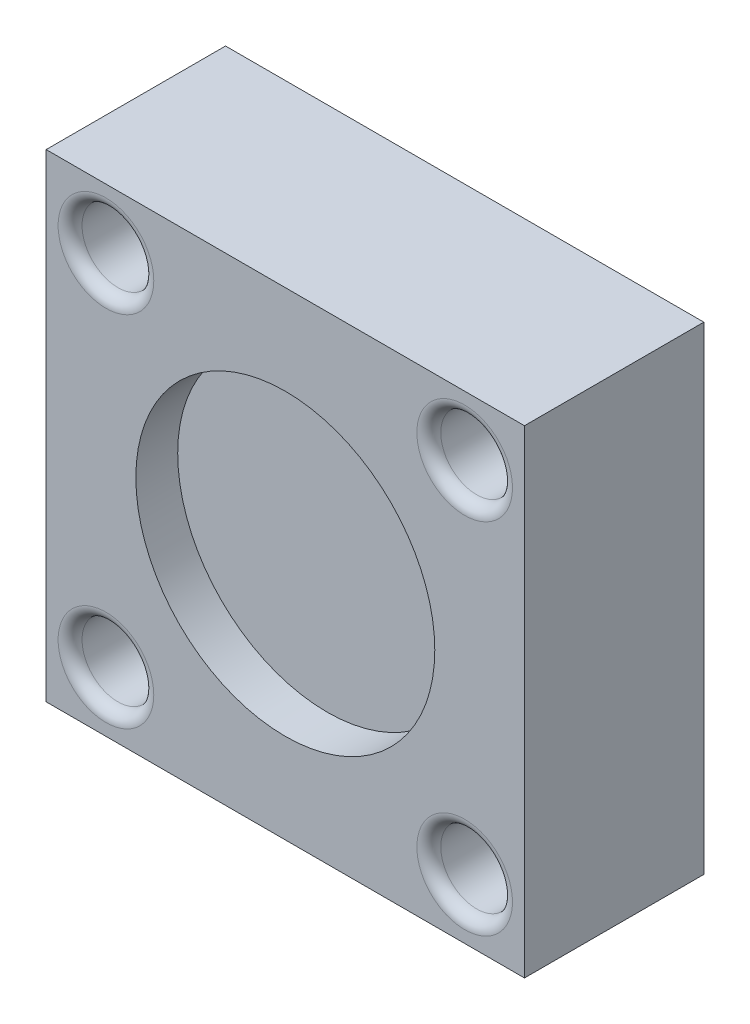
SolidWorks part; units mm, degrees
ref_plane "Front Plane" through (0, 0, 0) normal (0, 0, 1) x (1, 0, 0)
ref_plane "Top Plane" through (0, 0, 0) normal (0, 1, 0) x (1, 0, 0)
ref_plane "Right Plane" through (0, 0, 0) normal (1, 0, 0) x (0, 0, -1)
sketch "Sketch1" plane through (0, 0, 0) normal (0, 0, 1) x (1, 0, 0)
  line L1 (-20, 20) -> (20, 20)
  line L2 (-20, 20) -> (-20, -20)
  line L3 (-20, -20) -> (20, -20)
  line L4 (20, 20) -> (20, -20)
  line L5 (-20, 20) -> (20, -20) construction
  line L6 (-20, -20) -> (20, 20) construction
  point P0 (0, 0)
  dimension "D1" = 40
  dimension "D2" = 40
extrude "Boss-Extrude1" add sketch "Sketch1" along normal blind 15
sketch "Sketch3" plane through (0, 0, 15) normal (0, 0, 1) x (1, 0, 0)
  line L0 (20, -20) -> (20, 20) construction
  line L2 (-20, -20) -> (20, -20) construction
  line L3 (20, 20) -> (-20, 20) construction
  line L4 (20, 20) -> (-20, 20) construction
  line L5 (-20, 20) -> (-20, -20) construction
  line L6 (-20, -20) -> (20, -20) construction
  circle A0 centre (15, 15) radius 1.75
  circle A1 centre (15, -15) radius 1.75
  circle A2 centre (-15, 15) radius 1.75
  circle A3 centre (-15, -15) radius 1.75
  dimension "D1" = 3.5
  dimension "D2" = 3.5
  dimension "D3" = 3.5
  dimension "D4" = 3.5
  dimension "D5" = 5
  dimension "D6" = 5
  dimension "D7" = 5
  dimension "D8" = 5
  dimension "D9" = 5
  dimension "D10" = 5
  dimension "D11" = 5
  dimension "D12" = 5
extrude "Cut-Extrude2" cut sketch "Sketch3" against normal through all
sketch "Sketch4" plane through (0, 0, 15) normal (0, 0, 1) x (1, 0, 0)
  circle A0 centre (15, 15) radius 3
  circle A1 centre (15, -15) radius 3
  circle A2 centre (-15, -15) radius 3
  circle A3 centre (-15, 15) radius 3
  dimension "D1" = 6
  dimension "D2" = 6
  dimension "D3" = 6
  dimension "D4" = 6
extrude "Cut-Extrude3" cut sketch "Sketch4" against normal blind 7
fillet "Fillet1" radius 1 4 edges at (-12, -15, 15) (18, -15, 15) (18, 15, 15) (-12, 15, 15)
sketch "Sketch5" plane through (0, 0, 15) normal (0, 0, 1) x (1, 0, 0)
  circle A0 centre (0, 0) radius 12.5
  dimension "D1" = 25
extrude "Cut-Extrude4" cut sketch "Sketch5" against normal blind 3.5
